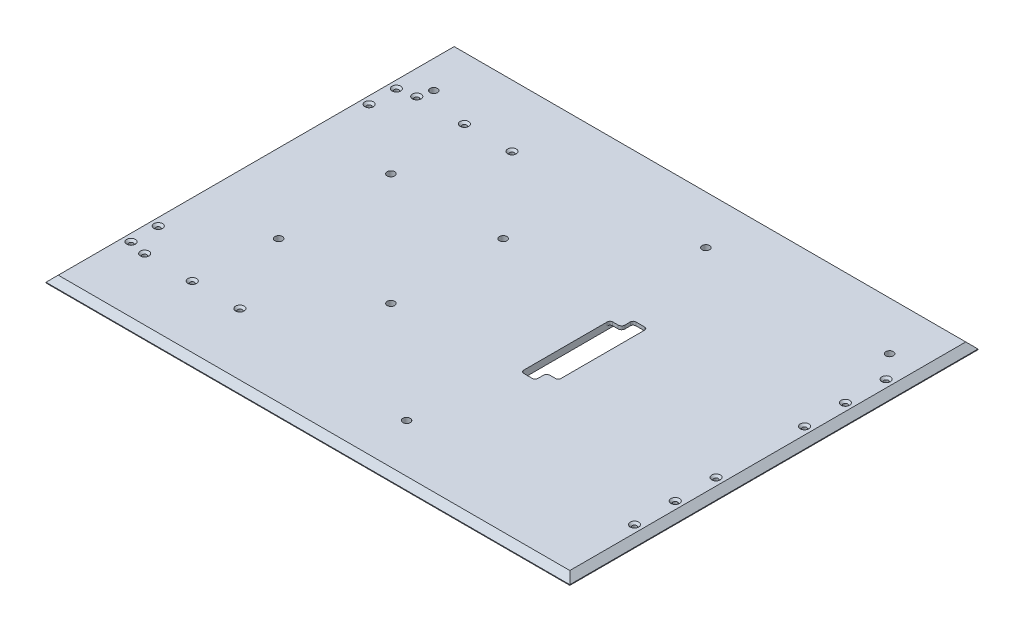
SolidWorks part; units mm, degrees
ref_plane "Front Plane" through (0, 0, 0) normal (0, 0, 1) x (1, 0, 0)
ref_plane "Top Plane" through (0, 0, 0) normal (0, 1, 0) x (1, 0, 0)
ref_plane "Right Plane" through (0, 0, 0) normal (1, 0, 0) x (0, 0, -1)
sketch "Sketch1" plane through (0, 0, 0) normal (0, 1, 0) x (1, 0, 0)
  line L1 (0, 0) -> (770, 0)
  line L2 (0, 0) -> (0, 600)
  line L3 (0, 600) -> (770, 600)
  line L4 (770, 0) -> (770, 600)
  dimension "D1" = 770
  dimension "D2" = 600
extrude "Boss-Extrude1" add sketch "Sketch1" along normal blind 10
chamfer "Chamfer1" distance 9 angle 45 4 edges at (385, 10, -600) (770, 10, -300) (385, 10, 0) (0, 10, -300)
sketch "Sketch2" plane through (0, 10, 0) normal (0, 1, 0) x (1, 0, 0)
  line L0 (472, 226) -> (472, 357)
  line L1 (472, 357) -> (489, 357)
  line L2 (489, 357) -> (489, 374)
  line L3 (489, 374) -> (510, 374)
  line L4 (510, 374) -> (510, 243)
  line L5 (510, 243) -> (493, 243)
  line L6 (493, 243) -> (493, 226)
  line L7 (493, 226) -> (472, 226)
  line L8 (0, 600) -> (770, 600) construction
  line L9 (770, 0) -> (0, 0) construction
  line L10 (770, 600) -> (770, 0) construction
  dimension "D1" = 226
  dimension "D2" = 226
  dimension "D3" = 38
  dimension "D4" = 17
  dimension "D5" = 17
  dimension "D6" = 17
  dimension "D7" = 17
  dimension "D8" = 260
extrude "Cut-Extrude1" cut sketch "Sketch2" against normal through all
fillet "Fillet1" radius 5 2 edges at (489, 5, -357) (493, 5, -243)
fillet "Fillet2" radius 4 6 edges at (510, 5, -374) (489, 5, -374) (472, 5, -357) (472, 5, -226) (510, 5, -243) (493, 5, -226)
sketch "Sketch3" plane through (0, 0, 0) normal (0, -1, 0) x (1, 0, 0)
  line L1 (505, -218) -> (477, -218)
  line L2 (510, -223) -> (510, -377)
  line L3 (505, -382) -> (477, -382)
  line L4 (472, -223) -> (472, -377)
  line L5 (510, -247) -> (510, -370) construction
  line L6 (472, -353) -> (472, -230) construction
  line L7 (0, 0) -> (770, 0) construction
  line L8 (770, -600) -> (0, -600) construction
  arc A0 (477, -382) -> (472, -377) centre (477, -377) cw
  arc A1 (510, -377) -> (505, -382) centre (505, -377) cw
  arc A2 (477, -218) -> (472, -223) centre (477, -223) ccw
  arc A3 (505, -218) -> (510, -223) centre (505, -223) cw
  dimension "D3" = 5
  dimension "D1" = 218
  dimension "D2" = 218
extrude "Cut-Extrude2" cut sketch "Sketch3" against normal blind 5
ref_plane "Plane1" through (385, 0, 0) normal (-1, 0, 0) x (0, 0, 1)
sketch "Sketch4" plane through (0, 0, 0) normal (0, -1, 0) x (1, 0, 0)
  line L2 (0, 0) -> (770, 0) construction
  line L3 (0, -600) -> (0, 0) construction
  circle A0 centre (50, -80) radius 10
  dimension "D3" = 20
  dimension "D1" = 80
  dimension "D2" = 50
ref_plane "Plane2" through (0, 0, -300) normal (0, 0, 1) x (1, 0, 0)
extrude "Boss-Extrude2" add sketch "Sketch4" along normal blind 9
mirror "Mirror1" about plane through (385, 0, 0) normal (-1, 0, 0) of "Boss-Extrude2"
mirror "Mirror2" about plane through (0, 0, -300) normal (0, 0, 1) of "Mirror1", "Boss-Extrude2"
sketch "Sketch5" plane through (0, 0, 0) normal (0, -1, 0) x (1, 0, 0)
  line L0 (0, 0) -> (770, 0) construction
  line L1 (770, 0) -> (770, -600) construction
  circle A0 centre (450, -80) radius 10
  dimension "D1" = 20
  dimension "D2" = 80
  dimension "D3" = 320
extrude "Boss-Extrude3" add sketch "Sketch5" along normal blind 9
mirror "Mirror3" about plane through (0, 0, -300) normal (0, 0, 1) of "Boss-Extrude3"
sketch "Sketch6" plane through (0, -9, 0) normal (0, -1, 0) x (1, 0, 0)
  circle A0 centre (50, -520) radius 5.5
  dimension "D1" = 11
extrude "Cut-Extrude3" cut sketch "Sketch6" against normal through all
mirror "Mirror4" about plane through (385, 0, 0) normal (-1, 0, 0) of "Cut-Extrude3"
sketch "Sketch7" plane through (0, -9, 0) normal (0, -1, 0) x (1, 0, 0)
  circle A0 centre (450, -520) radius 5.5
  dimension "D1" = 11
extrude "Cut-Extrude4" cut sketch "Sketch7" against normal through all
mirror "Mirror5" about plane through (0, 0, -300) normal (0, 0, 1) of "Cut-Extrude4"
sketch "Sketch8" plane through (0, -9, 0) normal (0, -1, 0) x (1, 0, 0)
  circle A0 centre (50, -80) radius 5.5
  dimension "D1" = 11
extrude "Boss-Extrude5" add sketch "Sketch8" along normal blind 15
chamfer "Chamfer2" distance 2.5 angle 45 1 edges at (50, -24, -85.5)
mirror "Mirror7" about plane through (385, 0, 0) normal (-1, 0, 0) of "Boss-Extrude5"
chamfer "Chamfer3" distance 2.5 angle 45 1 edges at (720, -24, -85.5)
hole_wizard "CSK for M6 Countersunk Flat Head Screw1" positions "Sketch9" profile "Sketch10" countersink size "M6" standard "ISO"
sketch "Sketch9" plane through (0, 10, 0) normal (0, 1, 0) x (1, 0, 0)
  point P3 (45, 500)
  point P9 (115, 500)
  point P12 (185, 500)
  point P18 (20, 145)
  point P21 (20, 105)
  point P24 (45, 100)
  point P30 (115, 100)
  point P33 (185, 100)
  point P36 (750, 115)
  point P39 (750, 175)
  point P42 (750, 235)
  point P45 (750, 365)
  point P48 (750, 425)
  point P51 (750, 485)
  point P56 (20, 495)
  point P59 (20, 455)
sketch "Sketch10" plane through (45, 10, -500) normal (1, 0, 0) x (0, 0, 1)
  line L0 (0, 0) -> (0, 24.9828)
  line L1 (0, 24.9828) -> (3.3, 23)
  line L2 (3.3, 23) -> (3.3, 3)
  line L3 (3.3, 3) -> (6.3, 0)
  line L5 (6.3, 0) -> (0, 0)
  line L6 (-3.3, 3) -> (-6.3, 0) construction
  line L10 (0, 24.9828) -> (-3.3, 23) construction
  line L11 (0, -6.35) -> (0, 107.95) construction
  dimension "Hole Dia." = 6.6
  dimension "Hole Depth" = 23
  dimension "Near C'Sink Dia." = 12.6
  dimension "Near C'Sink Angle" = 90
  dimension "Drill Angle" = 118
sketch "Sketch11" plane through (0, 10, 0) normal (0, 1, 0) x (1, 0, 0)
  circle A0 centre (289.5, 382.5) radius 5.5
  circle A1 centre (289.5, 217.5) radius 5.5
  circle A2 centre (124.5, 217.5) radius 5.5
  circle A3 centre (124.5, 382.5) radius 5.5
extrude "Cut-Extrude5" cut sketch "Sketch11" against normal through all
equation "\"2.5.00mm\"=5"
